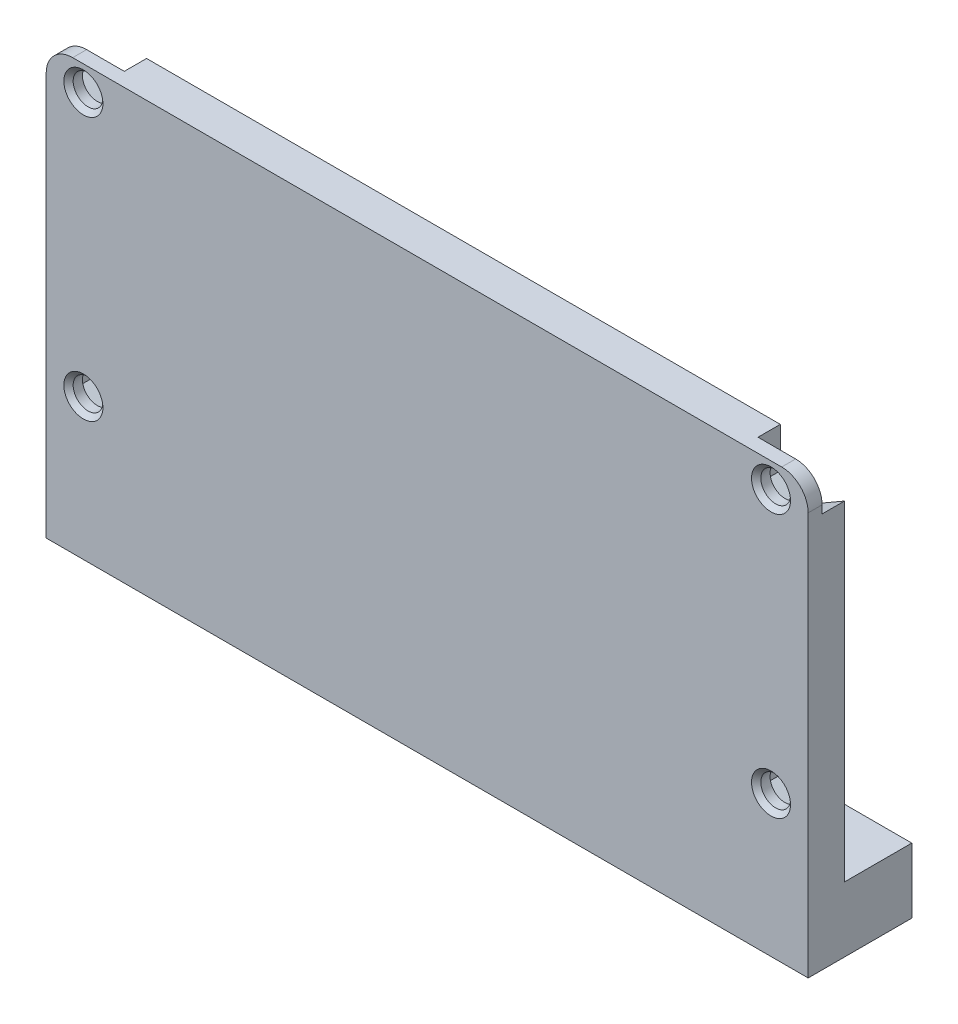
SolidWorks part; units mm, degrees
ref_plane "Front Plane" through (0, 0, 0) normal (0, 0, 1) x (1, 0, 0)
ref_plane "Top Plane" through (0, 0, 0) normal (0, 1, 0) x (1, 0, 0)
ref_plane "Right Plane" through (0, 0, 0) normal (1, 0, 0) x (0, 0, -1)
sketch "Sketch1" plane through (0, 0, 0) normal (0, 0, 1) x (1, 0, 0)
  line L1 (81, 11.6) -> (1, 11.6) construction
  line L3 (0, -35.2) -> (82, -35.2)
  line L5 (79.15, 11.6) -> (2.85, 11.6)
  line L9 (82, -35.2) -> (82, 8.75)
  line L10 (0, 8.75) -> (0, -35.2)
  line L11 (4, 8.9396) -> (4, -41.6656) construction
  circle A0 centre (4, 8.9396) radius 1.6 construction
  circle A1 centre (78, 8.9396) radius 1.6 construction
  circle A2 centre (4, -29.89) radius 1.6 construction
  circle A3 centre (4, 8.9396) radius 1.6
  circle A4 centre (78, 8.9396) radius 1.6
  arc A5 (82, 8.75) -> (79.15, 11.6) centre (79.15, 8.75) ccw
  arc A6 (0, 8.75) -> (2.85, 11.6) centre (2.85, 8.75) cw
  dimension "D1" = 46.8
  dimension "D2" = 2.85
extrude "Boss-Extrude1" add sketch "Sketch1" along normal blind 11.15 contours A3
sketch "Sketch2" plane through (0, 0, 0) normal (0, 0, -1) x (-1, 0, 0)
  line L0 (0, -49.6) -> (-82, -49.6) construction
  line L1 (0, -49.6) -> (-82, -49.6) construction
  line L2 (-82, -54.6) -> (0, -54.6)
  line L3 (-82, -34.6) -> (0, -34.6)
  line L4 (-82, -35.2) -> (-82, 8.75) construction
  line L5 (0, 8.75) -> (0, -35.2) construction
  line L7 (0, -34.6) -> (0, -35.2)
  line L8 (-82, -35.2) -> (-82, -34.6)
  line L9 (-82, -35.2) -> (0, -35.2)
  dimension "D1" = 5
  dimension "D2" = 20
extrude "Cut-Extrude1" cut sketch "Sketch2" against normal blind 8 contours L3 L7 L9 L8
sketch "Sketch3" plane through (0, -34.6, 0) normal (0, -1, 0) x (1, 0, 0)
  line L0 (10.85, 4) -> (10.85, 0)
  line L1 (14.15, 4) -> (14.15, 0)
  line L2 (16.75, 4) -> (16.75, 0)
  line L3 (23.25, 4) -> (23.25, 0)
  line L4 (0, 0) -> (82, 0)
  line L5 (82, 0) -> (82, 8)
  line L6 (82, 8) -> (0, 8)
  line L7 (0, 8) -> (0, 0)
  line L8 (10.85, 0) -> (14.15, 0)
  line L9 (82, 0) -> (82, 8)
  line L10 (82, 8) -> (0, 8)
  line L11 (0, 8) -> (0, 0)
  line L12 (25.85, 4) -> (25.85, 0)
  line L13 (29.15, 4) -> (29.15, 0)
  line L14 (25.85, 0) -> (82, 0)
  line L15 (16.75, 0) -> (23.25, 0)
  arc A0 (14.15, 4) -> (10.85, 4) centre (12.5, 4) ccw
  arc A1 (23.25, 4) -> (16.75, 4) centre (20, 4) ccw
  arc A2 (29.15, 4) -> (25.85, 4) centre (27.5, 4) ccw
  line M5 (0, 0) -> (82, 0)
  dimension "D2" = 3.3
  dimension "D3" = 3.3
  dimension "D4" = 15
  dimension "D5" = 7.5
  dimension "D6" = 6.5
  dimension "D7" = 20
  dimension "D1" = 0
extrude "Cut-Extrude2" cut sketch "Sketch3" against normal up to next (46.2 mm away) contours L13 A2 L12 M5 | A0 L0 L8 L1 | A1 L2 L15 L3
sketch "Sketch4" plane through (0, 11.6, 0) normal (0, 1, 0) x (1, 0, 0)
  line L0 (9.25, -4) -> (9.25, 0)
  line L1 (10.85, 0) -> (2.85, 0) construction
  line L2 (15.75, -4) -> (15.75, 0)
  line L3 (16.75, 0) -> (14.15, 0) construction
  line L4 (15.75, 0) -> (9.25, 0)
  line L5 (24.25, -4) -> (24.25, 0)
  line L6 (25.85, 0) -> (23.25, 0) construction
  line L7 (24.25, 0) -> (30.75, 0)
  line L8 (79.15, 0) -> (29.15, 0) construction
  line L9 (30.75, 0) -> (30.75, -4)
  arc A0 (10.85, -4) -> (14.15, -4) centre (12.5, -4) ccw construction
  arc A1 (25.85, -4) -> (29.15, -4) centre (27.5, -4) ccw construction
  arc A2 (10.85, -4) -> (14.15, -4) centre (12.5, -4) ccw construction
  arc A3 (25.85, -4) -> (29.15, -4) centre (27.5, -4) ccw construction
  arc A4 (9.25, -4) -> (15.75, -4) centre (12.5, -4) ccw
  arc A5 (24.25, -4) -> (30.75, -4) centre (27.5, -4) ccw
  dimension "D1" = 6.5
  dimension "D2" = 6.5
extrude "Cut-Extrude3" cut sketch "Sketch4" against normal offset from surface (40.2 mm away) 6 up to face at (25.25, -34.6, 2.9094)
sketch "Sketch6" plane through (0, 11.6, 0) normal (0, 1, 0) x (1, 0, 0)
  line L0 (15.75, -4) -> (15.75, 0) construction
  line L1 (24.25, 0) -> (24.25, -4) construction
  line L2 (15.75, -4) -> (15.75, 0)
  line L3 (24.25, 0) -> (24.25, -4)
  line L4 (12.5, -7.25) -> (0, -7.25)
  line L6 (0, -7.25) -> (0, 0.6518)
  line L7 (0, 0.6518) -> (15.75, 0.6518)
  line L8 (15.75, 0.6518) -> (15.75, 0)
  line L9 (27.5, -7.25) -> (41, -7.25)
  line L10 (41, -7.25) -> (41, 0)
  line L11 (79.15, 0) -> (30.75, 0) construction
  line L12 (41, 0) -> (24.25, 0)
  arc A0 (9.25, -4) -> (15.75, -4) centre (12.5, -4) ccw construction
  arc A1 (24.25, -4) -> (30.75, -4) centre (27.5, -4) ccw construction
  arc A2 (12.5, -7.25) -> (15.75, -4) centre (12.5, -4) ccw
  arc A3 (24.25, -4) -> (27.5, -7.25) centre (27.5, -4) ccw
  dimension "D1" = 41
extrude "Cut-Extrude5" cut sketch "Sketch6" against normal offset from surface (39.2 mm away) 7 up to face at (25.25, -34.6, 2.9094)
ref_plane "Plane1" through (41, 0, 0) normal (-1, 0, 0) x (0, 0, 1)
mirror "Mirror1" about plane through (41, 0, 0) normal (-1, 0, 0) of "Cut-Extrude5", "Cut-Extrude3", "Cut-Extrude2", "Cut-Extrude1"
sketch "Sketch8" plane through (0, 0, 8) normal (0, 0, -1) x (-1, 0, 0)
  line L4 (-82, -34.6) -> (-82, -35.2)
  line L5 (-82, -35.2) -> (0, -35.2)
  line L6 (0, -35.2) -> (0, -34.6)
  line L7 (0, -34.6) -> (-82, -34.6)
  line L8 (-82, -34.6) -> (-82, -35.2)
  line L9 (-82, -35.2) -> (0, -35.2)
  line L10 (0, -35.2) -> (0, -34.6)
  line L11 (0, -34.6) -> (-82, -34.6)
  dimension "D1" = 0
sketch "Sketch9" plane through (0, 0, 0) normal (-1, 0, 0) x (0, 0, 1)
  line L2 (7.25, 11.6) -> (0, 2.4)
  line L3 (0, 11.6) -> (7.25, 11.6)
sketch "Sketch12" plane through (0, 11.6, 0) normal (0, 1, 0) x (1, 0, 0)
  line L0 (16.75, -4) -> (16.75, 0)
  line L1 (16.75, 0) -> (18, 0)
  line L2 (23.25, 0) -> (23.25, -4)
  line L5 (22, 0) -> (23.25, 0)
  line L6 (58.75, -4) -> (58.75, 0)
  line L7 (58.75, 0) -> (60.05, 0)
  line L8 (65.25, 0) -> (65.25, -4) construction
  line L9 (65.25, 0) -> (65.25, -4)
  line L10 (60.05, 0) -> (60.155, -3.1064)
  line L11 (18, 0) -> (18.11, -3.0846)
  line L12 (63.95, 0) -> (65.25, 0)
  line L13 (22, 0) -> (21.89, -3.0846)
  line L15 (63.95, 0) -> (63.845, -3.1064)
  arc A0 (16.75, -4) -> (23.25, -4) centre (20, -4) ccw construction
  arc A1 (58.75, -4) -> (65.25, -4) centre (62, -4) ccw construction
  arc A2 (16.75, -4) -> (23.25, -4) centre (20, -4) ccw
  arc A3 (58.75, -4) -> (65.25, -4) centre (62, -4) ccw
  arc A4 (18.11, -3.0846) -> (21.89, -3.0846) centre (20, -4) ccw
  arc A5 (60.155, -3.1064) -> (63.845, -3.1064) centre (62, -4) ccw
  dimension "D1" = 1.25
  dimension "D2" = 4.1
  dimension "D3" = 1.3
  dimension "D4" = 1.3
  dimension "D5" = 1.25
extrude "Boss-Extrude2" add sketch "Sketch12" against normal offset from surface (32.2 mm away) 7 up to face at (41, -27.6, 3.9744)
chamfer "Chamfer3" distance 1.1 angle 45 3 edges at (58.75, -20.6, 2) (65.25, -20.6, 2) (62, -20.6, 7.25)
chamfer "Chamfer4" distance 1.1 angle 45 3 edges at (16.75, -20.6, 2) (23.25, -20.6, 2) (20, -20.6, 7.25)
extrude "Cut-Extrude12" cut sketch "Sketch9" against normal through all and the other way through all flip side to cut contours L3 L2
fillet "Fillet3" radius 15 10 edges at (60.1025, 4.371, 1.5532) (21.945, 4.3571, 1.5423) (20, 10.1407, 6.1) (18.055, 4.3571, 1.5423) (16.875, 2.4, 0) (23.125, 2.4, 0) (58.9, 2.4, 0) (65.1, 2.4, 0) (63.8975, 4.371, 1.5532) (62, 10.0772, 6.05)
sketch "Sketch13" plane through (0, 0, 7.25) normal (0, 0, -1) x (-1, 0, 0)
  circle A0 centre (-78, 8.9396) radius 2.85
  dimension "D1" = 5.7
sketch "Sketch14" plane through (0, 0, 11.15) normal (0, 0, 1) x (1, 0, 0)
  circle A0 centre (4, -19.4004) radius 1.6 construction
  circle A1 centre (4, -19.4004) radius 1.6
extrude "Cut-Extrude14" cut sketch "Sketch14" against normal through all contours A1
mirror "Mirror3" about plane through (41, 0, 0) normal (-1, 0, 0) of "Cut-Extrude14"
sketch "Sketch18" plane through (0, -27.6, 0) normal (0, 1, 0) x (1, 0, 0)
  line L6 (14.15, 0) -> (14.15, -4)
  line L7 (10.85, -4) -> (10.85, 0)
  line L8 (10.85, 0) -> (9.25, 0)
  line L9 (9.25, 0) -> (9.25, -4)
  line L10 (15.75, -4) -> (15.75, 0)
  line L11 (15.75, 0) -> (14.15, 0)
  line L12 (14.15, 0) -> (14.15, -1.2)
  line L13 (10.85, -1.2) -> (10.85, 0)
  line L14 (10.85, 0) -> (9.25, 0)
  line L15 (9.25, 0) -> (9.25, -4)
  line L16 (15.75, -4) -> (15.75, 0)
  line L17 (15.75, 0) -> (14.15, 0)
  line L18 (29.15, 0) -> (29.15, -4)
  line L19 (25.85, -4) -> (25.85, 0)
  line L20 (25.85, 0) -> (24.25, 0)
  line L21 (24.25, 0) -> (24.25, -4)
  line L22 (30.75, -4) -> (30.75, 0)
  line L23 (30.75, 0) -> (29.15, 0)
  line L24 (29.15, 0) -> (29.15, -1.2)
  line L25 (25.85, -1.2) -> (25.85, 0)
  line L26 (25.85, 0) -> (24.25, 0)
  line L27 (24.25, 0) -> (24.25, -4)
  line L28 (30.75, -4) -> (30.75, 0)
  line L29 (30.75, 0) -> (29.15, 0)
  arc A0 (10.85, -1.2) -> (9.25, -4) centre (12.5, -4) ccw
  arc A1 (15.75, -4) -> (14.15, -1.2) centre (12.5, -4) ccw
  arc A2 (10.85, -4) -> (14.15, -4) centre (12.5, -4) ccw
  arc A3 (9.25, -4) -> (15.75, -4) centre (12.5, -4) ccw
  arc A4 (25.85, -1.2) -> (24.25, -4) centre (27.5, -4) ccw
  arc A5 (30.75, -4) -> (29.15, -1.2) centre (27.5, -4) ccw
  arc A6 (25.85, -4) -> (29.15, -4) centre (27.5, -4) ccw
  arc A7 (24.25, -4) -> (30.75, -4) centre (27.5, -4) ccw
  dimension "D1" = 0
  dimension "D2" = 0
extrude "Boss-Extrude3" add sketch "Sketch18" against normal blind 3.5
mirror "Mirror5" about plane through (41, 0, 0) normal (-1, 0, 0) of "Boss-Extrude3"
sketch "Sketch19" plane through (0, 0, 7.25) normal (0, 0, -1) x (-1, 0, 0)
  circle A0 centre (-78, -19.4004) radius 2.85
extrude "Cut-Extrude16" cut sketch "Sketch8" against normal through all contours L11 L8 L9 L10
sketch "Sketch20" plane through (0, 0, 7.25) normal (0, 0, -1) x (-1, 0, 0)
  line L0 (-80.9, 12.2883) -> (-75.1, 12.2883)
  line L1 (-80.9, 12.2883) -> (-84.0715, 9.0964)
  line L4 (-84.0715, 9.0964) -> (-78, 5.591)
  line L5 (-78, 5.591) -> (-75.1, 7.2653)
  line L6 (-75.1, 7.2653) -> (-75.1, 12.2883)
  line L7 (-75.1, -21.0747) -> (-75.1, -17.726)
  line L8 (-75.1, -17.726) -> (-78, -16.0517)
  line L9 (-78, -16.0517) -> (-80.9, -17.726)
  line L10 (-80.9, -17.726) -> (-80.9, -21.0747)
  line L11 (-80.9, -21.0747) -> (-78, -22.749)
  line L12 (-78, -22.749) -> (-75.1, -21.0747)
  line L14 (-75.1, 10.614) -> (-78, 12.2883) [skipped]
  line L15 (-78, 12.2883) -> (-80.9, 10.614) [skipped]
  line L16 (-80.9, 8.9396) -> (-80.9, 7.2653) [skipped]
  circle A0 centre (-78, 8.9396) radius 1.6 construction
  circle A2 centre (-78, 8.9396) radius 2.9 construction
  circle A3 centre (-78, -19.4004) radius 2.9 construction
  dimension "D1" = 5.8
extrude "Cut-Extrude17" cut sketch "Sketch20" against normal blind 2.4
mirror "Mirror7" about plane through (41, 0, 0) normal (-1, 0, 0) of "Cut-Extrude17"
chamfer "Chamfer5" distance 0.5 angle 45 4 edges at (79.6, 8.9396, 11.15) (76.4, -19.4004, 11.15) (5.6, -19.4004, 11.15) (5.6, 8.9396, 11.15)
